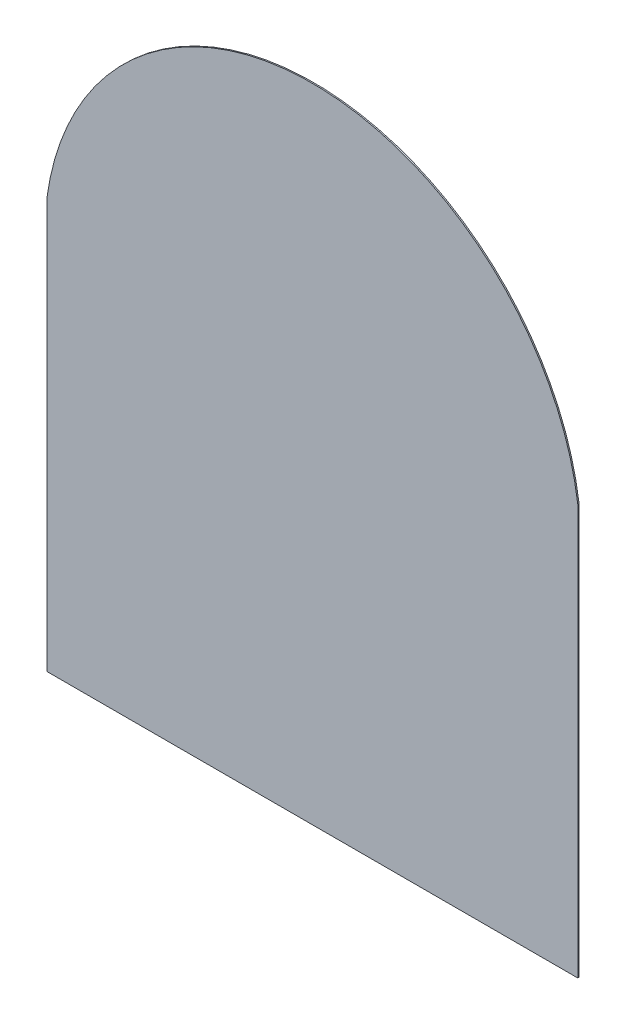
SolidWorks part; units mm, degrees
ref_plane "Front Plane" through (0, 0, 0) normal (0, 0, 1) x (1, 0, 0)
ref_plane "Top Plane" through (0, 0, 0) normal (0, 1, 0) x (1, 0, 0)
ref_plane "Right Plane" through (0, 0, 0) normal (1, 0, 0) x (0, 0, -1)
sketch "Sketch1" plane through (0, 0, 0) normal (0, 0, 1) x (1, 0, 0)
  line L2 (1030, 796) -> (1030, -796)
  line L3 (1030, -796) -> (-1030, -796)
  line L4 (-1030, 796) -> (-1030, -796)
  line L5 (1030, 796) -> (-1030, -796) construction
  line L6 (1030, -796) -> (-1030, 796) construction
  arc A1 (-1030, 796) -> (1030, 796) centre (0, 656.6111) cw
  point P0 (0, 0)
  point P1 (0, 0)
  point P8 (0, 0)
  point P9 (0, 0)
  point P10 (0, 1696)
  dimension "D1" = 2060
  dimension "D2" = 900
  dimension "D3" = 1592
extrude "Boss-Extrude1" add sketch "Sketch1" along normal mid plane 5
